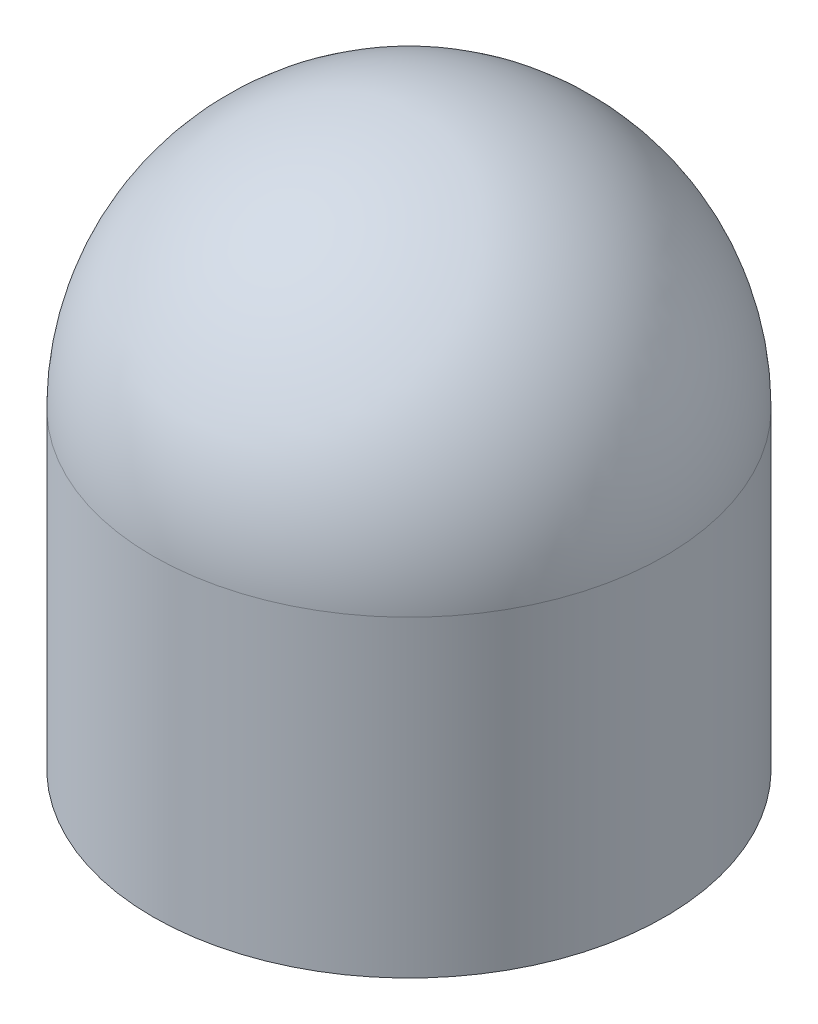
SolidWorks part; units mm, degrees
ref_plane "Front Plane" through (0, 0, 0) normal (0, 0, 1) x (1, 0, 0)
ref_plane "Top Plane" through (0, 0, 0) normal (0, 1, 0) x (1, 0, 0)
ref_plane "Right Plane" through (0, 0, 0) normal (1, 0, 0) x (0, 0, -1)
sketch "Sketch1" plane through (0, 0, 0) normal (0, 1, 0) x (1, 0, 0)
  circle A0 centre (0, 0) radius 5
extrude "Boss-Extrude1" add sketch "Sketch1" along normal blind 6.1
sketch "Sketch2" plane through (0, 6.1, 0) normal (0, 1, 0) x (1, 0, 0)
  line L0 (0, 5) -> (0, -5)
  circle A0 centre (0, 0) radius 5 construction
  arc A1 (0, 5) -> (0, -5) centre (0, 0) ccw
revolve "Revolve1" add sketch "Sketch2" angle 360 mid plane about L0
